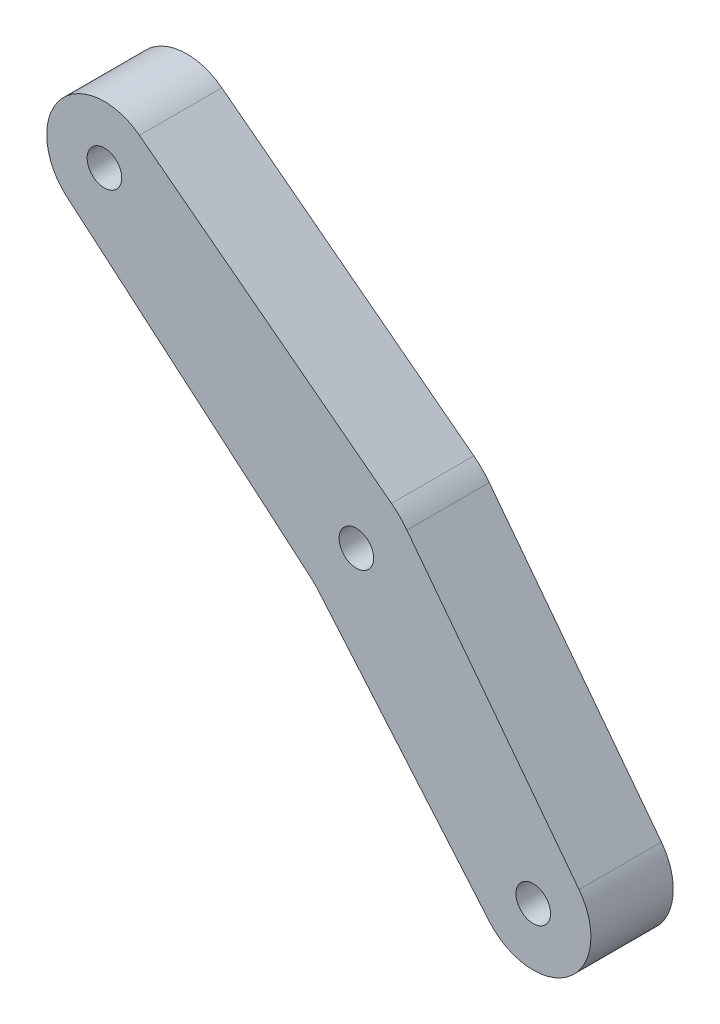
SolidWorks part; units mm, degrees
ref_plane "Alzado" through (0, 0, 0) normal (0, 0, 1) x (1, 0, 0)
ref_plane "Planta" through (0, 0, 0) normal (0, 1, 0) x (1, 0, 0)
ref_plane "Vista lateral" through (0, 0, 0) normal (1, 0, 0) x (0, 0, -1)
sketch "Croquis1" plane through (0, 0, 0) normal (0, 0, 1) x (1, 0, 0)
  line L1 (-58.8013, 52.4008) -> (-28.2084, 29.0035)
  line L2 (-5.4385, -0.2112) -> (-26.3383, 27.1329)
  line L3 (-16.3314, -8.9981) -> (-37.0116, 15.3082)
  line L4 (-38.1456, 16.4425) -> (-67.5914, 41.5104)
  circle A0 centre (-63.0538, 46.8405) radius 2.1
  circle A1 centre (-32.4725, 22.157) radius 2.1
  circle A2 centre (-11, -4.462) radius 2.1
  arc A3 (-58.8013, 52.4008) -> (-67.5914, 41.5104) centre (-63.0538, 46.8405) ccw
  arc A4 (-5.4385, -0.2112) -> (-16.3314, -8.9981) centre (-11, -4.462) cw
  arc A6 (-26.3383, 27.1329) -> (-28.2084, 29.0035) centre (-34.2834, 21.0603) ccw
  arc A7 (-37.0116, 15.3082) -> (-38.1456, 16.4425) centre (-44.6279, 8.8281) ccw
  dimension "D1" = 4.2
extrude "Saliente-Extruir1" add sketch "Croquis1" along normal blind 10
